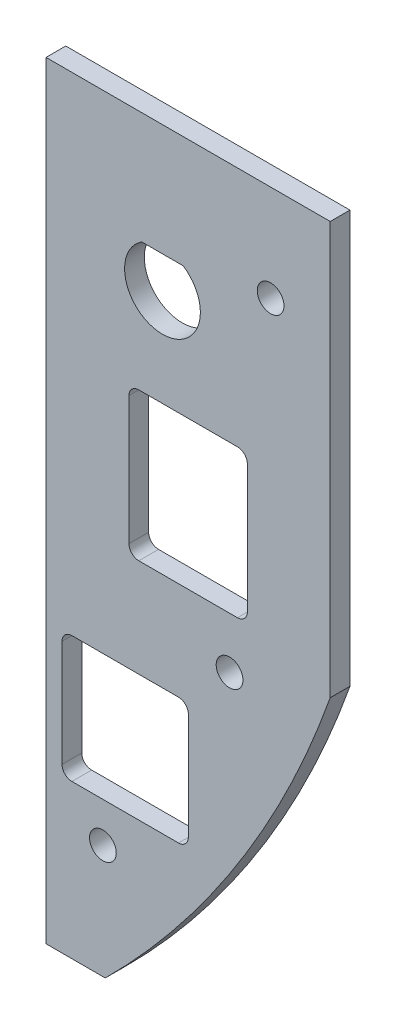
SolidWorks part; units mm, degrees
ref_plane "Front Plane" through (0, 0, 0) normal (0, 0, 1) x (1, 0, 0)
ref_plane "Top Plane" through (0, 0, 0) normal (0, 1, 0) x (1, 0, 0)
ref_plane "Right Plane" through (0, 0, 0) normal (1, 0, 0) x (0, 0, -1)
sketch "Sketch1" plane through (0, 0, 0) normal (0, 0, 1) x (1, 0, 0)
  line L8 (0, -17.78) -> (0, -141.2875)
  line L9 (0, -141.2875) -> (9.525, -141.2875)
  line L10 (45.72, -84.1375) -> (45.72, -17.78)
  line L11 (45.72, -17.78) -> (0, -17.78)
  circle A0 centre (18.7325, -40.894) radius 1.1901
  arc A2 (9.525, -141.2875) -> (45.72, -84.1375) centre (-97.9169, -33.2042) ccw
  circle A3 centre (18.7325, -40.894) radius 6.35 construction
extrude "Boss-Extrude1" add sketch "Sketch1" against normal blind 3.175
sketch "Sketch11" plane through (20.8448, -43.5748, 0) normal (0, 0, 1) x (1, 0, 0)
  line L0 (-5.4434, 7.7862) -> (1.2188, 7.7862)
  arc A0 (-5.4434, 7.7862) -> (1.2188, 7.7862) centre (-2.1123, 2.6808) ccw
  point P4 (-2.1123, -3.4152)
  dimension "D1" = 12.192
  dimension "D2" = 11.2014
extrude "Cut-Extrude1" cut sketch "Sketch11" against normal through all
other "Smart-Feature1<SxAL-1>"
sketch "Sketch12" plane through (0, 0, 0) normal (0, 0, 1) x (1, 0, 0)
  line L1 (13.335, -56.642) -> (32.385, -56.642)
  line L2 (13.335, -56.642) -> (13.335, -80.4545)
  line L3 (13.335, -80.4545) -> (32.385, -80.4545)
  line L4 (32.385, -56.642) -> (32.385, -80.4545)
  line L5 (22.86, -80.4545) -> (22.86, -56.642) construction
  line L6 (13.335, -68.5483) -> (32.385, -68.5483) construction
  point P152 (22.86, -68.5483)
extrude "Cut-Extrude2" cut sketch "Sketch12" against normal through all
hole_wizard "Hole1" [suppressed] positions "Sketch14" profile "Sketch13" legacy
sketch "Sketch14" plane through (0, 0, -3.175) normal (0, 0, -1) x (-1, 0, 0)
  point P0 (-34.29, -58.547)
  point P3 (-11.43, -78.5495)
  point P6 (-19.8535, -94.4687)
  point P8 (-5.5488, -118.2724)
sketch "Sketch13" plane through (34.29, -58.547, -3.175) normal (1, 0, 0) x (0, 1, 0)
  line L0 (0, 0) -> (0, 2.921)
  line L1 (0, 2.921) -> (1.4986, 2.921)
  line L2 (1.4986, 2.921) -> (1.6383, 0)
  line L3 (1.6383, 0) -> (0, 0)
  line L4 (0, 110) -> (0, -10) construction
  dimension "Minor Diameter" = 2.9972
  dimension "Depth" = 2.921
  dimension "Major Diameter" = 3.2766
hole_wizard "#2 Clearance Hole1" [suppressed] positions "Sketch16" profile "Sketch15" hole size "#2" standard "ANSI Inch"
sketch "Sketch16" [suppressed] plane through (0, 0, -0.254) normal (0, 0, -1) x (-1, 0, 0)
  point P0 (-34.29, -58.547)
  point P3 (-11.43, -78.5495)
sketch "Sketch15" plane through (34.29, -58.547, -0.254) normal (1, 0, 0) x (0, 1, 0)
  line L0 (0, 0) -> (0, 36.576)
  line L1 (0, 36.576) -> (1.3525, 36.576)
  line L2 (1.3525, 36.576) -> (1.3525, 0)
  line L5 (1.3525, 0) -> (0, 0)
  line L10 (0, 36.576) -> (-1.3526, 36.576) construction
  line L11 (0, -6.35) -> (0, 107.95) construction
  dimension "Hole Dia." = 2.7051
  dimension "Hole Depth" = 36.576
  dimension "Drill Angle" = 180
sketch "Sketch17" plane through (0, 0, 0) normal (0, 0, 1) x (1, 0, 0)
  line L1 (22.8917, -116.5825) -> (2.5717, -116.5825)
  line L2 (22.8917, -116.5825) -> (22.8917, -96.2625)
  line L3 (22.8917, -96.2625) -> (2.5717, -96.2625)
  line L4 (2.5717, -116.5825) -> (2.5717, -96.2625)
  line L5 (12.7317, -96.2625) -> (12.7317, -116.5825) construction
  line L6 (22.8917, -106.4225) -> (2.5717, -106.4225) construction
  point P192 (12.7317, -106.4225)
  dimension "D1" = 20.32
  dimension "D2" = 20.32
extrude "Cut-Extrude3" cut sketch "Sketch17" against normal through all
fillet "Fillet1" radius 1.5875 8 edges at (32.385, -56.642, -1.5875) (32.385, -80.4545, -1.5875) (13.335, -56.642, -1.5875) (13.335, -80.4545, -1.5875) (2.5717, -116.5825, -1.5875) (22.8917, -116.5825, -1.5875) (22.8917, -96.2625, -1.5875) (2.5717, -96.2625, -1.5875)
hole_wizard "#6 Clearance Hole1" positions "Sketch19" profile "Sketch18" hole size "#6" standard "ANSI Inch" end condition through all
sketch "Sketch19" plane through (0, 0, 0) normal (0, 0, 1) x (1, 0, 0)
  point P0 (9.144, -122.9995)
  point P3 (29.5275, -88.7095)
  point P6 (36.1315, -33.274)
sketch "Sketch18" plane through (9.144, -122.9995, 0) normal (1, 0, 0) x (0, -1, 0)
  line L0 (0, 0) -> (0, 3.175)
  line L1 (0, 3.175) -> (2.1526, 3.175)
  line L2 (2.1526, 3.175) -> (2.1526, 0)
  line L5 (2.1526, 0) -> (0, 0)
  line L11 (0, -6.35) -> (0, 107.95) construction
  dimension "Thru Hole Dia." = 4.3053
  dimension "Thru Hole Depth" = 3.175
